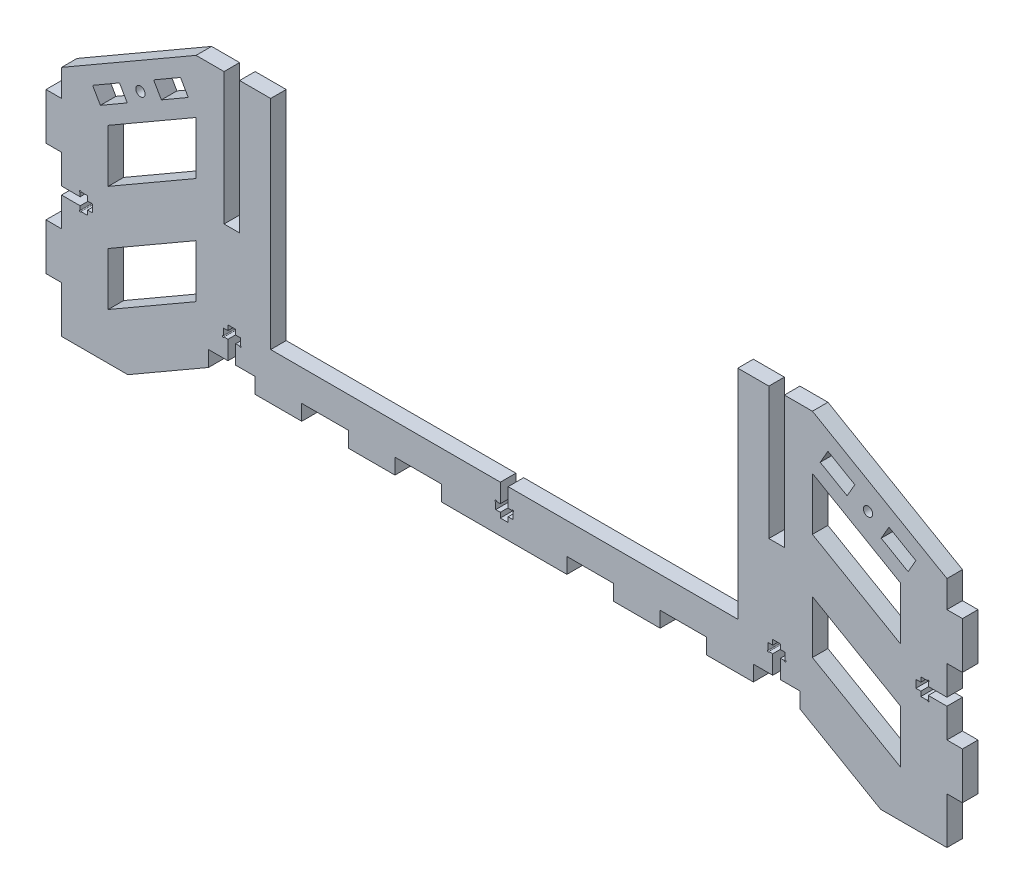
SolidWorks part; units mm, degrees
material "PMMA"
ref_plane "Front Plane" through (0, 0, 0) normal (0, 0, 1) x (1, 0, 0)
ref_plane "Top Plane" through (0, 0, 0) normal (0, 1, 0) x (1, 0, 0)
ref_plane "Right Plane" through (0, 0, 0) normal (1, 0, 0) x (0, 0, -1)
sketch "Schizzo1" plane through (0, 0, 0) normal (0, 0, 1) x (1, 0, 0)
  line L0 (-142.5, 75) -> (-142.5, 66.3397)
  line L1 (-142.5, 0) -> (142.5, 0)
  line L2 (142.5, 75) -> (142.5, 66.3397)
  line L3 (142.5, 75) -> (99.1987, 100)
  line L4 (99.1987, 100) -> (-99.1987, 100)
  line L5 (-99.1987, 100) -> (-142.5, 75)
  line L6 (95.1795, 85) -> (-95.1795, 85) construction
  line L7 (-95.1795, 85) -> (-127.5, 66.3397) construction
  line L8 (-127.5, 66.3397) -> (-127.5, 15) construction
  line L9 (-127.5, 15) -> (127.5, 15) construction
  line L10 (127.5, 15) -> (127.5, 66.3397) construction
  line L11 (127.5, 66.3397) -> (95.1795, 85) construction
  line L12 (-95.1795, 85) -> (-95.1795, 15) construction
  line L13 (95.1795, 85) -> (95.1795, 15) construction
  line L14 (-127.5, 66.3397) -> (127.5, 66.3397) construction
  line L15 (-142.5, 66.3397) -> (-147.5, 66.3397)
  line L16 (-147.5, 66.3397) -> (-147.5, 51.3397)
  line L17 (-147.5, 51.3397) -> (-142.5, 51.3397)
  line L18 (-142.5, 51.3397) -> (-142.5, 30)
  line L19 (-142.5, 30) -> (-147.5, 30)
  line L20 (-147.5, 30) -> (-147.5, 15)
  line L21 (-147.5, 15) -> (-142.5, 15)
  line L22 (-142.5, 15) -> (-142.5, 0)
  line L23 (-142.5, 75) -> (-142.5, 0) construction
  line L24 (142.5, 66.3397) -> (147.5, 66.3397)
  line L25 (142.5, 0) -> (142.5, 75) construction
  line L26 (147.5, 66.3397) -> (147.5, 51.3397)
  line L27 (147.5, 51.3397) -> (142.5, 51.3397)
  line L28 (142.5, 51.3397) -> (142.5, 30)
  line L29 (142.5, 30) -> (147.5, 30)
  line L30 (147.5, 30) -> (147.5, 15)
  line L31 (147.5, 15) -> (142.5, 15)
  line L32 (142.5, 15) -> (142.5, 0)
  point P2 (0, 0)
  dimension "D1" = 5
  dimension "D2" = 285
  dimension "D3" = 100
  dimension "D4" = 75
  dimension "D5" = 198.3975
  dimension "D7" = 190.359
  dimension "D8" = 15
  dimension "D9" = 150
  dimension "D10" = 21.3397
  dimension "D6" = 15
extrude "Estrusione-Estrusione1" add sketch "Schizzo1" along normal blind 5
sketch "Schizzo2" plane through (0, 0, 0) normal (0, 0, 1) x (1, 0, 0)
  line L0 (-99.1987, 82.6795) -> (-127.5, 66.3397)
  line L1 (-113.3494, 74.5096) -> (-120.8494, 87.5) construction
  line L2 (0, 0) -> (0, 100) construction
  line L3 (99.1987, 100) -> (-99.1987, 100) construction
  line L4 (-127.5, 49.3301) -> (-127.5, 66.3397)
  line L5 (99.1987, 31.3397) -> (99.1987, 48.3494)
  line L6 (-99.1987, 100) -> (-99.1987, 0) construction
  line L7 (99.1987, 31.3397) -> (127.5, 15)
  line L8 (127.5, 32.0096) -> (127.5, 15)
  line L9 (-95.1795, 15) -> (-121.1603, 0)
  line L10 (99.1987, 48.3494) -> (127.5, 32.0096)
  line L11 (-121.1603, 0) -> (121.1603, 0)
  line L12 (121.1603, 0) -> (95.1795, 15)
  line L13 (95.1795, 15) -> (-95.1795, 15)
  line L14 (-142.5, 0) -> (142.5, 0) construction
  line L15 (-99.1987, 31.3397) -> (-127.5, 15)
  line L16 (-99.1987, 65.6699) -> (-99.1987, 82.6795)
  line L17 (99.1987, 65.6699) -> (99.1987, 82.6795)
  line L18 (127.5, 49.3301) -> (99.1987, 65.6699)
  line L19 (127.5, 49.3301) -> (127.5, 66.3397)
  line L20 (-127.5, 49.3301) -> (-99.1987, 65.6699)
  line L21 (-99.1987, 48.3494) -> (-127.5, 32.0096)
  line L22 (-127.5, 32.0096) -> (-127.5, 15)
  line L23 (-99.1987, 31.3397) -> (-99.1987, 48.3494)
  line L24 (99.1987, 82.6795) -> (127.5, 66.3397)
  line L25 (-99.1987, 100) -> (-142.5, 75) construction
  line L26 (-127.5, 66.3397) -> (-135, 79.3301) construction
  line L27 (-132.5, 75) -> (-123.8397, 80)
  line L28 (-132.5, 75) -> (-130, 70.6699)
  line L29 (-130, 70.6699) -> (-121.3397, 75.6699)
  line L30 (-123.8397, 80) -> (-121.3397, 75.6699)
  line L31 (-104.1987, 91.3397) -> (-101.6987, 87.0096)
  line L32 (-104.1987, 91.3397) -> (-112.859, 86.3397)
  line L33 (-112.859, 86.3397) -> (-110.359, 82.0096)
  line L34 (-101.6987, 87.0096) -> (-110.359, 82.0096)
  line L35 (132.5, 75) -> (130, 70.6699)
  line L36 (130, 70.6699) -> (121.3397, 75.6699)
  line L37 (123.8397, 80) -> (121.3397, 75.6699)
  line L38 (132.5, 75) -> (123.8397, 80)
  line L39 (104.1987, 91.3397) -> (112.859, 86.3397)
  line L40 (104.1987, 91.3397) -> (101.6987, 87.0096)
  line L41 (101.6987, 87.0096) -> (110.359, 82.0096)
  line L42 (112.859, 86.3397) -> (110.359, 82.0096)
  circle A0 centre (-117.0994, 81.0048) radius 1.5
  circle A1 centre (117.0994, 81.0048) radius 1.5
  point P42 (-131.25, 72.8349)
  point P44 (-131.25, 72.8349)
  point P51 (-117.0994, 81.0048)
  dimension "D4" = 3
  dimension "D1" = 15
  dimension "D2" = 10
  dimension "D3" = 5
extrude "Taglio-Estrusione2" cut sketch "Schizzo2" along direction (0, 0, 1) on the side of the normal through all
sketch "Schizzo5" plane through (0, 0, 0) normal (0, 0, 1) x (1, 0, 0)
  line L0 (-95.1795, 15) -> (-95.1795, 20)
  line L1 (-95.1795, 20) -> (-80.1795, 20)
  line L2 (-80.1795, 20) -> (-80.1795, 15)
  line L3 (-80.1795, 15) -> (-95.1795, 15)
  line L4 (-65.1795, 20) -> (-65.1795, 15)
  line L5 (-65.1795, 15) -> (-50.1795, 15)
  line L6 (-50.1795, 15) -> (-50.1795, 20)
  line L7 (-50.1795, 20) -> (-65.1795, 20)
  line L8 (-35.1795, 15) -> (-35.1795, 20)
  line L9 (-35.1795, 20) -> (-20.1795, 20)
  line L10 (-20.1795, 20) -> (-20.1795, 15)
  line L11 (-20.1795, 15) -> (-35.1795, 15)
  line L12 (-127.5, 15) -> (127.5, 15) construction
  line L13 (-95.1795, 85) -> (-95.1795, 15) construction
  line L14 (0, 15) -> (0, 100) construction
  line L15 (35.1795, 15) -> (35.1795, 20)
  line L16 (20.1795, 15) -> (35.1795, 15)
  line L17 (20.1795, 20) -> (20.1795, 15)
  line L18 (35.1795, 20) -> (20.1795, 20)
  line L19 (50.1795, 15) -> (50.1795, 20)
  line L20 (65.1795, 15) -> (50.1795, 15)
  line L21 (65.1795, 20) -> (65.1795, 15)
  line L22 (50.1795, 20) -> (65.1795, 20)
  line L23 (95.1795, 15) -> (95.1795, 20)
  line L24 (80.1795, 15) -> (95.1795, 15)
  line L25 (80.1795, 20) -> (80.1795, 15)
  line L26 (95.1795, 20) -> (80.1795, 20)
  line L27 (-95.1795, 57.5) -> (95.1795, 57.5) construction
  line L28 (-95.1795, 15) -> (-121.1603, 0) construction
  line L29 (95.1795, 85) -> (95.1795, 15) construction
  line L30 (99.1987, 100) -> (-99.1987, 100) construction
  line L31 (90.1795, 100) -> (85.1795, 100)
  line L32 (-90.1795, 100) -> (-85.1795, 100)
  line L33 (-90.1795, 100) -> (-90.1795, 57.5)
  line L34 (-90.1795, 57.5) -> (-85.1795, 57.5)
  line L35 (-85.1795, 100) -> (-85.1795, 57.5)
  line L36 (90.1795, 100) -> (90.1795, 57.5)
  line L37 (90.1795, 57.5) -> (85.1795, 57.5)
  line L38 (85.1795, 100) -> (85.1795, 57.5)
  line L40 (-75.1795, 100) -> (75.1795, 100)
  line L41 (-75.1795, 100) -> (-75.1795, 30)
  line L42 (-75.1795, 30) -> (75.1795, 30)
  line L43 (75.1795, 100) -> (75.1795, 30)
  dimension "D1" = 5
  dimension "D2" = 15
  dimension "D3" = 15
  dimension "D4" = 15
  dimension "D5" = 42.5
  dimension "D6" = 42.5
  dimension "D7" = 5
  dimension "D8" = 5
  dimension "D9" = 10
  dimension "D10" = 10
  dimension "D11" = 15
  dimension "D12" = 190.359
  dimension "D13" = 40.359
extrude "Taglio-Estrusione3" cut sketch "Schizzo5" along direction (0, 0, 1) on the side of the normal through all
sketch "Schizzo6" plane through (0, 0, 0) normal (0, 0, 1) x (1, 0, 0)
  line L0 (-142.5, 51.3397) -> (-142.5, 30) construction
  line L1 (-142.5, 40.6699) -> (-120, 40.6699) construction
  line L2 (-142.5, 41.9199) -> (-136.5, 41.9199)
  line L3 (-136.5, 41.9199) -> (-136.5, 43.4199)
  line L4 (-136.5, 43.4199) -> (-134.1, 43.4199)
  line L5 (-134.1, 43.4199) -> (-134.1, 41.9199)
  line L6 (-134.1, 41.9199) -> (-132.5, 41.9199)
  line L7 (-132.5, 41.9199) -> (-132.5, 39.4199)
  line L8 (-132.5, 39.4199) -> (-134.1, 39.4199)
  line L9 (-134.1, 39.4199) -> (-134.1, 37.9199)
  line L10 (-134.1, 37.9199) -> (-136.5, 37.9199)
  line L11 (-136.5, 37.9199) -> (-136.5, 39.4199)
  line L12 (-136.5, 39.4199) -> (-142.5, 39.4199)
  line L13 (-142.5, 39.4199) -> (-142.5, 41.9199)
  line L14 (0, 0) -> (0, 100) construction
  line L15 (134.1, 43.4199) -> (134.1, 41.9199)
  line L16 (136.5, 43.4199) -> (134.1, 43.4199)
  line L17 (136.5, 41.9199) -> (136.5, 43.4199)
  line L18 (142.5, 41.9199) -> (136.5, 41.9199)
  line L19 (142.5, 39.4199) -> (142.5, 41.9199)
  line L20 (136.5, 39.4199) -> (142.5, 39.4199)
  line L21 (136.5, 37.9199) -> (136.5, 39.4199)
  line L22 (134.1, 37.9199) -> (136.5, 37.9199)
  line L23 (134.1, 39.4199) -> (134.1, 37.9199)
  line L24 (132.5, 39.4199) -> (134.1, 39.4199)
  line L25 (132.5, 41.9199) -> (132.5, 39.4199)
  line L26 (134.1, 41.9199) -> (132.5, 41.9199)
  line L27 (-90.1795, 57.5) -> (-85.1795, 57.5) construction
  line L28 (-87.6795, 57.5) -> (-87.6795, 2.5) construction
  line L29 (-80.1795, 20) -> (-95.1795, 20) construction
  line L30 (85.1795, 57.5) -> (90.1795, 57.5) construction
  line L31 (87.6795, 57.5) -> (87.6795, 20) construction
  line L32 (95.1795, 20) -> (80.1795, 20) construction
  line L33 (-87.6795, 20) -> (-87.6795, 30) construction
  line L34 (-88.9295, 20) -> (-88.9295, 26)
  line L35 (-88.9295, 26) -> (-90.4295, 26)
  line L36 (-90.4295, 26) -> (-90.4295, 28.4)
  line L37 (-90.4295, 28.4) -> (-88.9295, 28.4)
  line L38 (-88.9295, 28.4) -> (-88.9295, 30)
  line L39 (-88.9295, 30) -> (-86.4295, 30)
  line L40 (-86.4295, 30) -> (-86.4295, 28.4)
  line L41 (-86.4295, 28.4) -> (-84.9295, 28.4)
  line L42 (-84.9295, 28.4) -> (-84.9295, 26)
  line L43 (-84.9295, 26) -> (-86.4295, 26)
  line L44 (-86.4295, 26) -> (-86.4295, 20)
  line L45 (-86.4295, 20) -> (-88.9295, 20)
  line L46 (86.4295, 20) -> (88.9295, 20)
  line L47 (86.4295, 26) -> (86.4295, 20)
  line L48 (84.9295, 26) -> (86.4295, 26)
  line L49 (84.9295, 28.4) -> (84.9295, 26)
  line L50 (86.4295, 28.4) -> (84.9295, 28.4)
  line L51 (86.4295, 30) -> (86.4295, 28.4)
  line L52 (88.9295, 30) -> (86.4295, 30)
  line L53 (88.9295, 28.4) -> (88.9295, 30)
  line L54 (90.4295, 28.4) -> (88.9295, 28.4)
  line L55 (90.4295, 26) -> (90.4295, 28.4)
  line L56 (88.9295, 26) -> (90.4295, 26)
  line L57 (88.9295, 20) -> (88.9295, 26)
  line L58 (0, 32.4779) -> (0, 27.5221) construction
  line L59 (0, 20) -> (0, 30) construction
  line L60 (-1.25, 20) -> (-1.25, 21.6)
  line L61 (-1.25, 21.6) -> (-2.75, 21.6)
  line L62 (-2.75, 21.6) -> (-2.75, 24)
  line L63 (-2.75, 24) -> (-1.25, 24)
  line L64 (-1.25, 24) -> (-1.25, 30)
  line L65 (-1.25, 30) -> (1.25, 30)
  line L66 (1.25, 30) -> (1.25, 24)
  line L67 (1.25, 24) -> (2.75, 24)
  line L68 (2.75, 24) -> (2.75, 21.6)
  line L69 (2.75, 21.6) -> (1.25, 21.6)
  line L70 (1.25, 21.6) -> (1.25, 20)
  line L71 (1.25, 20) -> (-1.25, 20)
  line L73 (-75.1795, 30) -> (75.1795, 30) construction
  dimension "D1" = 5.5
  dimension "D2" = 2.5
  dimension "D3" = 1.25
  dimension "D4" = 2.75
  dimension "D5" = 2.4
  dimension "D6" = 10
  dimension "D7" = 5.5
  dimension "D8" = 2.5
  dimension "D9" = 1.25
  dimension "D10" = 2.75
  dimension "D11" = 2.4
  dimension "D12" = 10
  dimension "D13" = 90
  dimension "D14" = 90
  dimension "D15" = 5.5
  dimension "D16" = 2.5
  dimension "D17" = 1.25
  dimension "D18" = 2.75
  dimension "D19" = 2.4
  dimension "D20" = 10
  dimension "D21" = 90
  dimension "D22" = 90
  dimension "D23" = 6
  dimension "D24" = 6
  dimension "D25" = 6
extrude "Taglio-Estrusione4" cut sketch "Schizzo6" along direction (0, 0, 1) on the side of the normal through all
sketch "Schizzo7" plane through (0, 0, 5) normal (0, 0, 1) x (1, 0, 0)
  circle A0 centre (-136.5, 43.4199) radius 0.25
  circle A1 centre (-136.5, 37.9199) radius 0.25
  circle A2 centre (-90.4295, 26) radius 0.25
  circle A3 centre (-84.9295, 26) radius 0.25
  circle A4 centre (-2.75, 24) radius 0.25
  circle A5 centre (2.75, 24) radius 0.25
  circle A6 centre (84.9295, 26) radius 0.25
  circle A7 centre (90.4295, 26) radius 0.25
  circle A8 centre (136.5, 43.4199) radius 0.25
  circle A9 centre (136.5, 37.9199) radius 0.25
  dimension "D1" = 0.5
  dimension "D2" = 0.5
  dimension "D3" = 0.5
  dimension "D4" = 0.5
  dimension "D5" = 0.5
extrude "Taglio-Estrusione5" cut sketch "Schizzo7" against normal blind 10
equation "\"Thickness\"=5"
equation "\"D1@Estrusione-Estrusione1\"=\"Thickness\""
equation "\"D1@Schizzo5\"=\"Thickness\""
equation "\"D7@Schizzo5\"=\"Thickness\""
equation "\"D9@Schizzo5\"=2*\"Thickness\""
equation "\"D10@Schizzo5\"=2*\"Thickness\""
equation "\"D1@Schizzo1\"=\"Thickness\""
equation "\"D3@Schizzo2\"=\"Thickness\""
